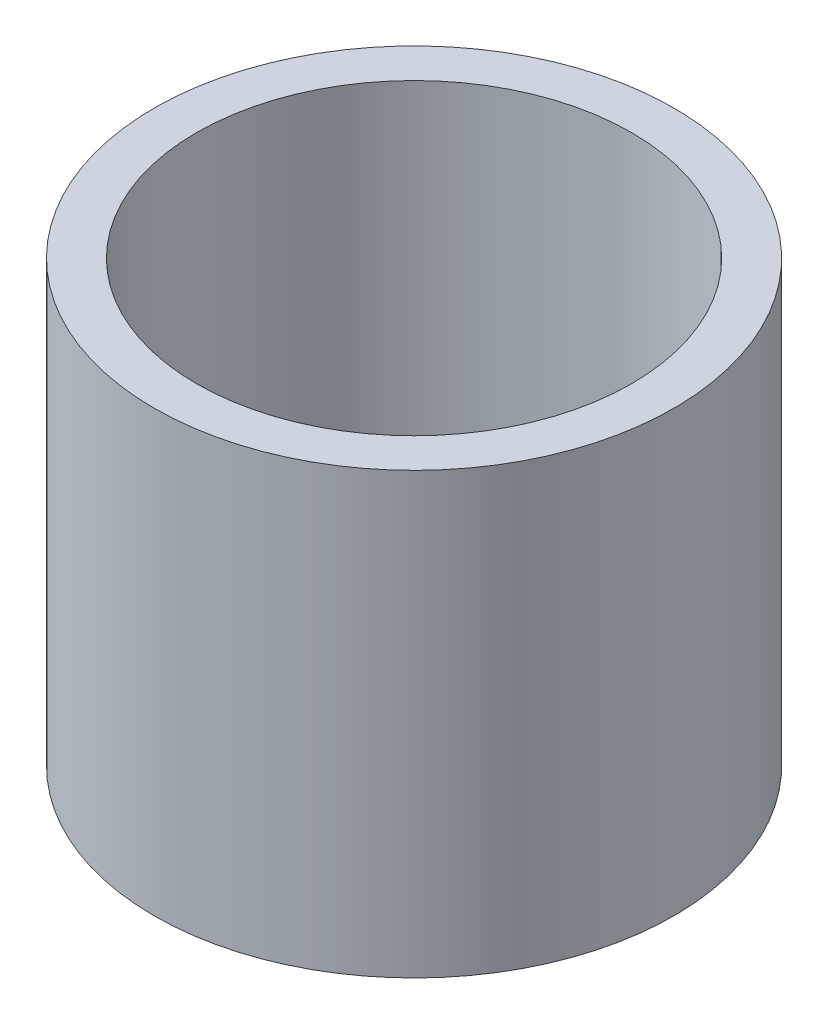
SolidWorks part; units mm, degrees
ref_plane "Front Plane" through (0, 0, 0) normal (0, 0, 1) x (1, 0, 0)
ref_plane "Top Plane" through (0, 0, 0) normal (0, 1, 0) x (1, 0, 0)
ref_plane "Right Plane" through (0, 0, 0) normal (1, 0, 0) x (0, 0, -1)
sketch "Sketch2" plane through (0, 0, 0) normal (0, 1, 0) x (1, 0, 0)
  circle A0 centre (0, 0) radius 11.684
  circle A1 centre (0, 0) radius 5.08
  circle A2 centre (0, 0.2907) radius 9.652
extrude "Boss-Extrude2" add sketch "Sketch2" along normal blind 1.9812 contours A2 A1 | A0 A2
sketch "Sketch4" plane through (0, 1.9812, 0) normal (0, 1, 0) x (1, 0, 0)
  circle A0 centre (0, 0) radius 9.779
  circle A1 centre (0, 0) radius 11.684
extrude "Boss-Extrude3" add sketch "Sketch4" along normal blind 17.78
